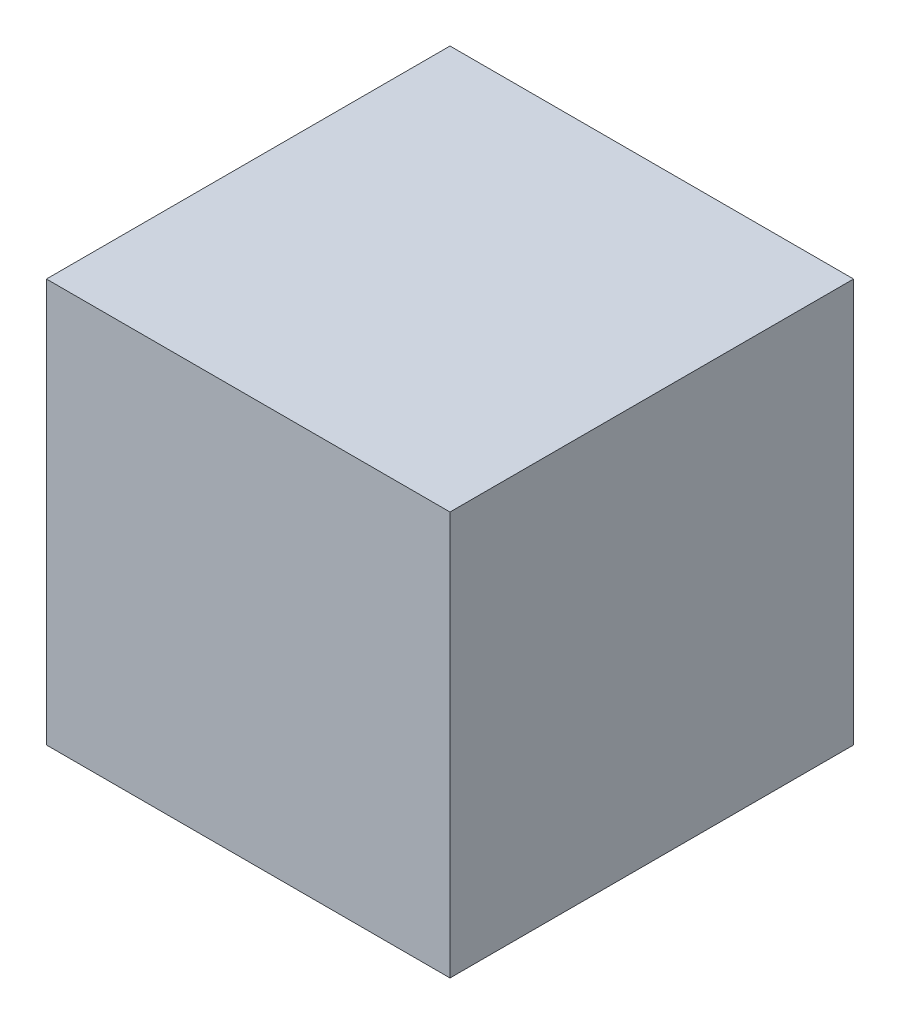
SolidWorks part; units mm, degrees
ref_plane "Front Plane" through (0, 0, 0) normal (0, 0, 1) x (1, 0, 0)
ref_plane "Top Plane" through (0, 0, 0) normal (0, 1, 0) x (1, 0, 0)
ref_plane "Right Plane" through (0, 0, 0) normal (1, 0, 0) x (0, 0, -1)
sketch "Sketch2" plane through (0, 0, 0) normal (0, 1, 0) x (1, 0, 0)
  line L1 (-5, -5) -> (5, -5)
  line L2 (-5, -5) -> (-5, 5)
  line L3 (-5, 5) -> (5, 5)
  line L4 (5, -5) -> (5, 5)
  line L5 (0, 5) -> (0, -5) construction
  line L6 (-5, 0) -> (5, 0) construction
  point P0 (0, 0)
  dimension "D1" = 10
  dimension "D2" = 10
extrude "Boss-Extrude1" add sketch "Sketch2" along normal blind 10
